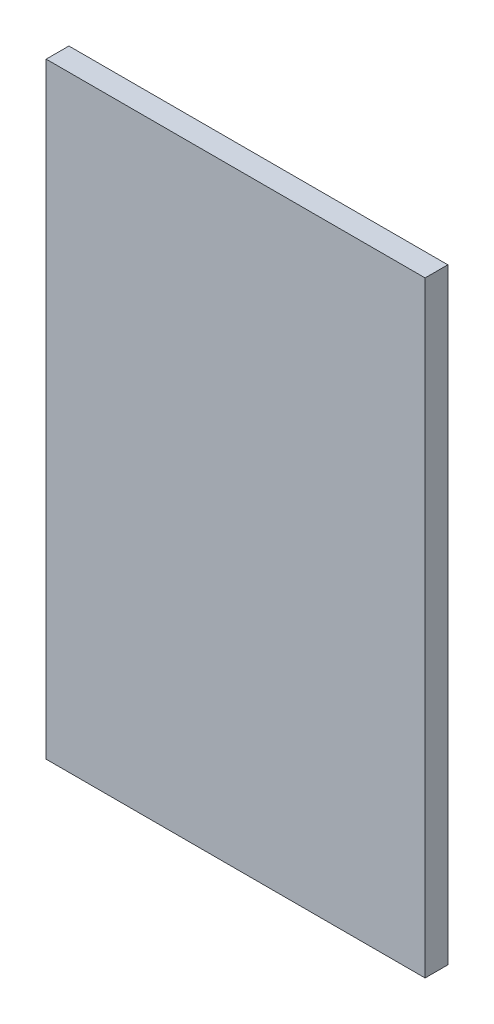
SolidWorks part; units mm, degrees
ref_plane "Front Plane" through (0, 0, 0) normal (0, 0, 1) x (1, 0, 0)
ref_plane "Top Plane" through (0, 0, 0) normal (0, 1, 0) x (1, 0, 0)
ref_plane "Right Plane" through (0, 0, 0) normal (1, 0, 0) x (0, 0, -1)
sketch "Sketch1" plane through (0, 0, 0) normal (0, 1, 0) x (1, 0, 0)
  line L1 (-250, 15) -> (250, 15)
  line L2 (-250, 15) -> (-250, -15)
  line L3 (-250, -15) -> (250, -15)
  line L4 (250, 15) -> (250, -15)
  line L5 (-250, 15) -> (250, -15) construction
  line L6 (-250, -15) -> (250, 15) construction
  point P0 (0, 0)
  dimension "D1" = 30
  dimension "D2" = 500
extrude "Boss-Extrude1" add sketch "Sketch1" along normal blind 800
